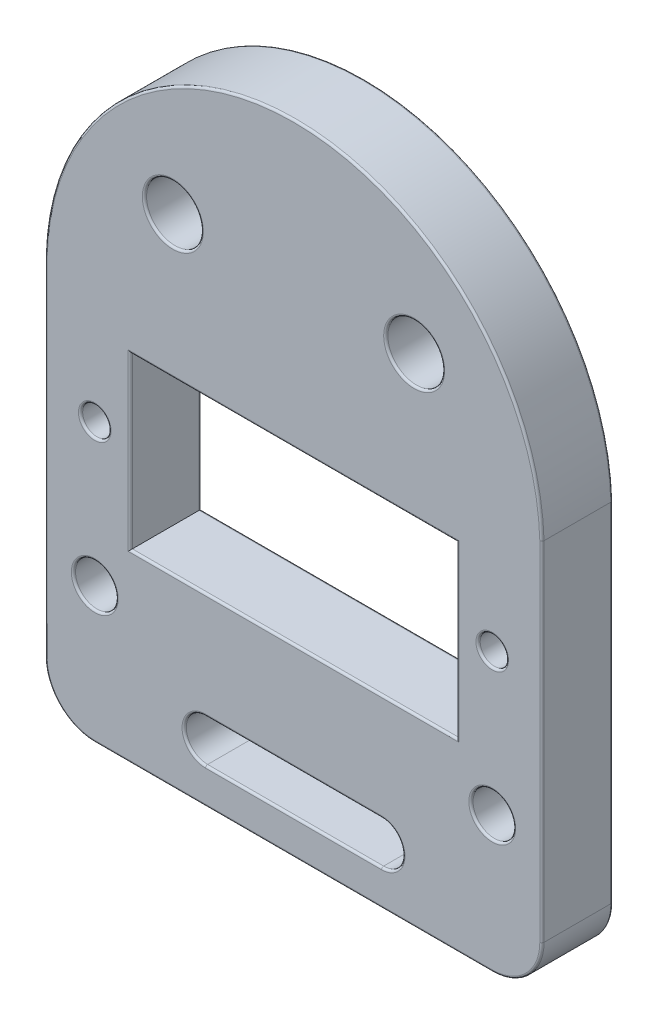
SolidWorks part; units mm, degrees
ref_plane "Ön Düzlem" through (0, 0, 0) normal (0, 0, 1) x (1, 0, 0)
ref_plane "Üst Düzlem" through (0, 0, 0) normal (0, 1, 0) x (1, 0, 0)
ref_plane "Sağ Düzlem" through (0, 0, 0) normal (1, 0, 0) x (0, 0, -1)
sketch "Sketch1" plane through (0, 0, 0) normal (0, 0, 1) x (1, 0, 0)
  line L0 (0, -19) -> (0, 26) construction
  line L1 (-11.5, -6) -> (11.5, -6)
  line L2 (-11.5, -6) -> (-11.5, 6)
  line L3 (-11.5, 6) -> (11.5, 6)
  line L4 (11.5, -6) -> (11.5, 6)
  line L5 (-11.5, -6) -> (11.5, 6) construction
  line L6 (-11.5, 6) -> (11.5, -6) construction
  line L7 (-6.2, -15) -> (6.2, -15) construction
  line L8 (-17.5, 9) -> (17.5, 9) construction
  line L9 (-17.5, 9) -> (-17.5, -19)
  line L10 (-17.5, -19) -> (17.5, -19)
  line L11 (17.5, 9) -> (17.5, -19)
  line L12 (-6.2, -13.5) -> (6.2, -13.5)
  line L13 (-6.2, -16.5) -> (6.2, -16.5)
  arc A0 (-17.5, 9) -> (17.5, 9) centre (0, 8.4926) cw
  circle A1 centre (-8.5, 16) radius 2
  circle A2 centre (-14, 0.588) radius 1
  circle A3 centre (-14, -9.412) radius 1.5
  circle A4 centre (8.5, 16) radius 2
  circle A5 centre (14, 0.588) radius 1
  circle A6 centre (14, -9.412) radius 1.5
  arc A7 (-6.2, -13.5) -> (-6.2, -16.5) centre (-6.2, -15) ccw
  arc A8 (6.2, -16.5) -> (6.2, -13.5) centre (6.2, -15) ccw
  point P0 (0, 0)
  point P12 (0, -19)
  point P21 (0, -15)
  dimension "D7" = 2
  dimension "D10" = 3
  dimension "D12" = 4
  dimension "D15" = 1.5
  dimension "D1" = 12
  dimension "D2" = 23
  dimension "D3" = 45
  dimension "D4" = 13
  dimension "D5" = 28
  dimension "D6" = 35
  dimension "D8" = 2.5
  dimension "D9" = 10
  dimension "D11" = 10
  dimension "D13" = 8.5
  dimension "D14" = 12.4
  dimension "D16" = 4
extrude "Boss-Extrude1" add sketch "Sketch1" along normal blind 5
fillet "Fillet1" radius 3.5 2 edges at (17.5, -19, 2.5) (-17.5, -19, 2.5)
fillet "Fillet2" radius 0.15 40 edges at (7.7, -15, 0) (0, -16.5, 0) (-7.7, -15, 0) (0, -13.5, 0) (12.5, -9.412, 0) (6.5, 16, 0) (-13, 0.588, 0) (-11.5, 0, 0) (0, 6, 0) (11.5, 0, 0) (0, -6, 0) (0, 26, 0) (-17.5, -3.25, 0) (-16.4749, -17.9749, 0) (0, -19, 0) (16.4749, -17.9749, 0) (17.5, -3.25, 0) (-6.5, 16, 0) (-12.5, -9.412, 0) (13, 0.588, 0) (0, -16.5, 5) (7.7, -15, 5) (0, -13.5, 5) (-7.7, -15, 5) (-16.4749, -17.9749, 5) (-17.5, -3.25, 5) (0, 26, 5) (17.5, -3.25, 5) (16.4749, -17.9749, 5) (0, -19, 5) (0, 6, 5) (-11.5, 0, 5) (0, -6, 5) (11.5, 0, 5) (-6.5, 16, 5) (-13, 0.588, 5) (-12.5, -9.412, 5) (6.5, 16, 5) (13, 0.588, 5) (12.5, -9.412, 5)
